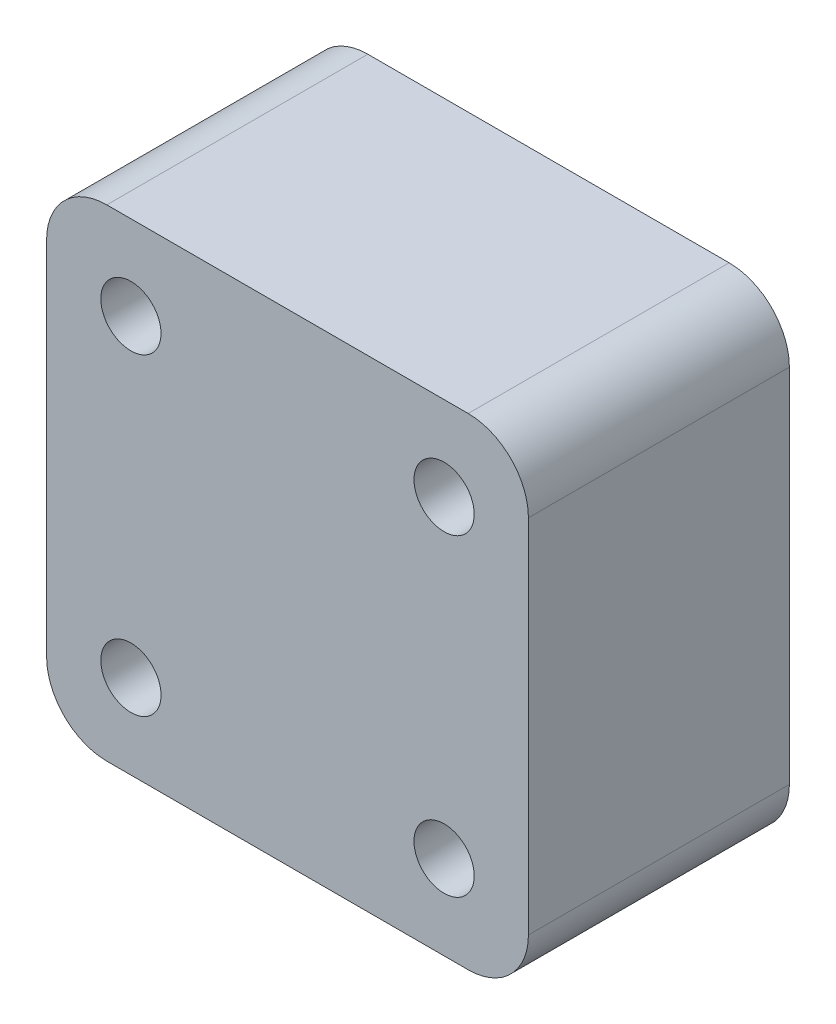
SolidWorks part; units mm, degrees
ref_plane "Plano frontal" through (0, 0, 0) normal (0, 0, 1) x (1, 0, 0)
ref_plane "Plano superior" through (0, 0, 0) normal (0, 1, 0) x (1, 0, 0)
ref_plane "Plano direito" through (0, 0, 0) normal (1, 0, 0) x (0, 0, -1)
sketch "Esboço1" plane through (0, 0, 0) normal (0, 0, 1) x (1, 0, 0)
  line L1 (-24, -24) -> (24, -24)
  line L2 (-24, -24) -> (-24, 24)
  line L3 (-24, 24) -> (24, 24)
  line L4 (24, -24) -> (24, 24)
  line L5 (-24, -24) -> (24, 24) construction
  line L6 (-24, 24) -> (24, -24) construction
  point P0 (0, 0)
  dimension "D1" = 48
  dimension "D2" = 48
extrude "Ressalto-extrusão1" add sketch "Esboço1" along normal blind 26
sketch "Esboço3" plane through (0, 0, 26) normal (0, 0, 1) x (1, 0, 0)
  line L0 (0, 24) -> (0, -24) construction
  line L1 (24, 24) -> (-24, 24) construction
  line L2 (-24, -24) -> (24, -24) construction
  line L3 (24, 0) -> (-24, 0) construction
  line L4 (24, -24) -> (24, 24) construction
  line L5 (-24, 24) -> (-24, -24) construction
  circle A0 centre (-15.6, -15.6) radius 3
  circle A1 centre (-15.6, 15.6) radius 3
  circle A2 centre (15.6, -15.6) radius 3
  circle A3 centre (15.6, 15.6) radius 3
  dimension "D2" = 6
  dimension "D1" = 31.2
  dimension "D3" = 31.2
extrude "Corte-extrusão2" cut sketch "Esboço3" against normal through all
fillet "Filete2" radius 6 4 edges at (24, -24, 13) (-24, -24, 13) (24, 24, 13) (-24, 24, 13)
